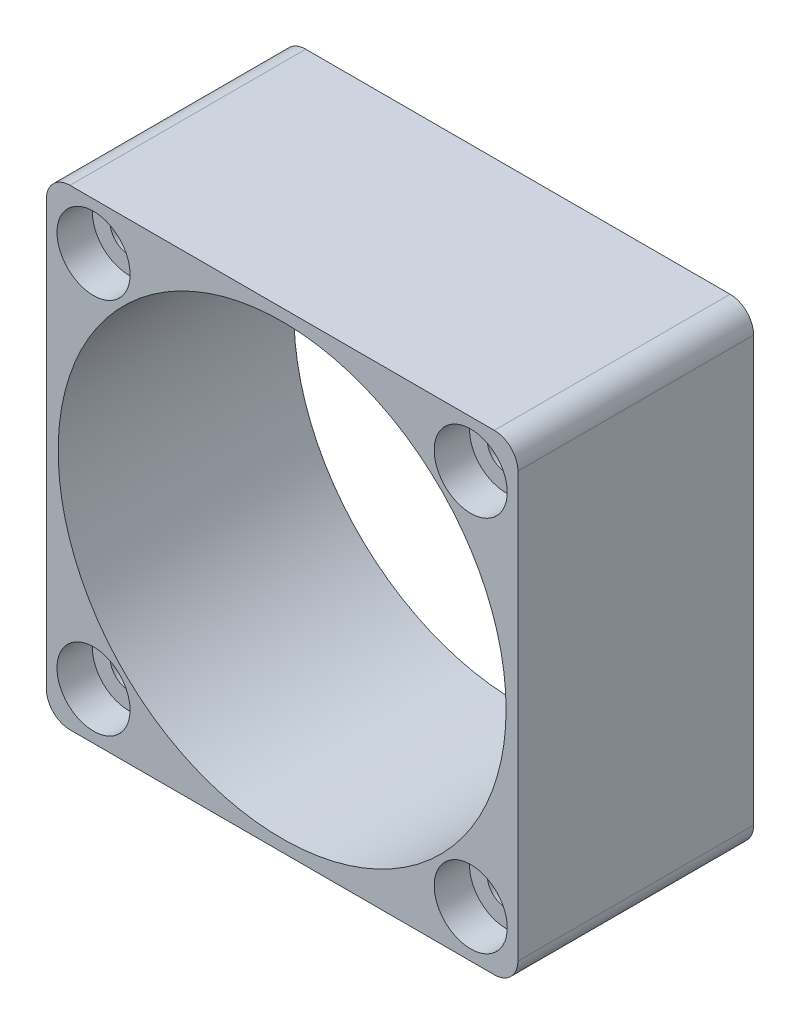
SolidWorks part; units mm, degrees
material "PUR"
ref_plane "Front Plane" through (0, 0, 0) normal (0, 0, 1) x (1, 0, 0)
ref_plane "Top Plane" through (0, 0, 0) normal (0, 1, 0) x (1, 0, 0)
ref_plane "Right Plane" through (0, 0, 0) normal (1, 0, 0) x (0, 0, -1)
sketch "Sketch1" plane through (0, 0, 0) normal (0, 0, 1) x (1, 0, 0)
  line L1 (-20, 20) -> (20, 20)
  line L2 (-20, 20) -> (-20, -20)
  line L3 (-20, -20) -> (20, -20)
  line L4 (20, 20) -> (20, -20)
  line L5 (-20, 20) -> (20, -20) construction
  line L6 (-20, -20) -> (20, 20) construction
  point P0 (0, 0)
  dimension "D1" = 40
extrude "Boss-Extrude1" add sketch "Sketch1" along normal blind 20
sketch "Sketch2" plane through (0, 0, 20) normal (0, 0, 1) x (1, 0, 0)
  line L1 (-16, -16) -> (16, -16) construction
  line L2 (-16, -16) -> (-16, 16) construction
  line L3 (-16, 16) -> (16, 16) construction
  line L4 (16, -16) -> (16, 16) construction
  line L5 (-16, -16) -> (16, 16) construction
  line L6 (-16, 16) -> (16, -16) construction
  circle A0 centre (0, 0) radius 19
  circle A1 centre (-16, 16) radius 1.6
  circle A2 centre (16, 16) radius 1.6
  circle A3 centre (16, -16) radius 1.6
  circle A4 centre (-16, -16) radius 1.6
  dimension "D1" = 38
  dimension "D3" = 3.2
  dimension "D2" = 32
extrude "Cut-Extrude1" cut sketch "Sketch2" against normal through all
fillet "Fillet1" radius 2 4 edges at (-20, -20, 10) (-20, 20, 10) (20, -20, 10) (20, 20, 10)
sketch "Sketch3" plane through (0, 0, 20) normal (0, 0, 1) x (1, 0, 0)
  circle A0 centre (-16, -16) radius 3.1
  circle A1 centre (16, -16) radius 3.1
  circle A2 centre (16, 16) radius 3.1
  circle A3 centre (-16, 16) radius 3.1
  dimension "D1" = 6.2
extrude "Cut-Extrude2" cut sketch "Sketch3" against normal blind 3
